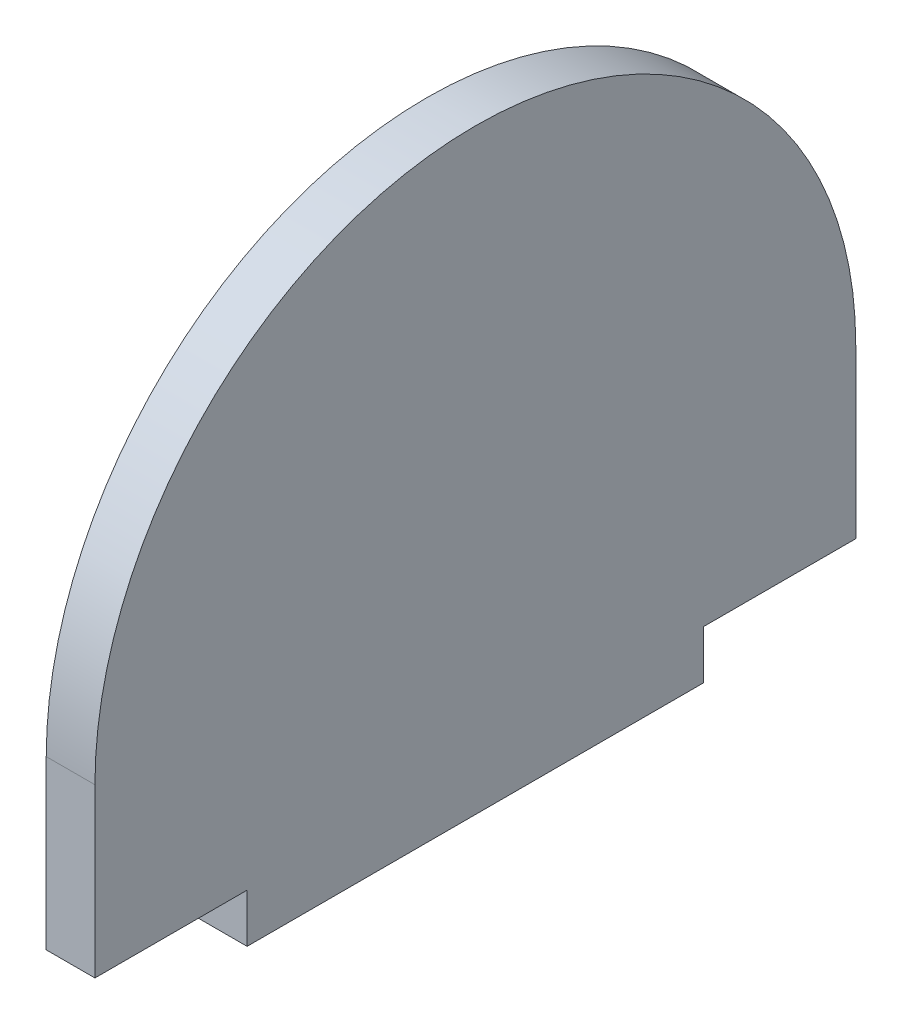
SolidWorks part; units mm, degrees
ref_plane "Front Plane" through (0, 0, 0) normal (0, 0, 1) x (1, 0, 0)
ref_plane "Top Plane" through (0, 0, 0) normal (0, 1, 0) x (1, 0, 0)
ref_plane "Right Plane" through (0, 0, 0) normal (1, 0, 0) x (0, 0, -1)
sketch "Sketch1" plane through (0, 0, 0) normal (1, 0, 0) x (0, 0, -1)
  line L0 (20.8415, -18.3879) -> (30.8415, -18.3879)
  line L1 (-19.1585, -7.3879) -> (-19.1585, -18.3879)
  line L2 (-19.1585, -18.3879) -> (-9.1585, -18.3879)
  line L3 (30.8415, -7.3879) -> (30.8415, -18.3879)
  line L4 (-9.1585, -18.3879) -> (-9.1585, -21.5879)
  line L5 (-9.1585, -21.5879) -> (20.8415, -21.5879)
  line L6 (20.8415, -21.5879) -> (20.8415, -18.3879)
  arc A0 (-19.1585, -7.3879) -> (30.8415, -7.3879) centre (5.8415, -7.3879) cw
  dimension "D1" = 30
extrude "Boss-Extrude1" add sketch "Sketch1" along normal blind 3.2 contours L1 L2 L4 L5 L6 L0 L3 A0
